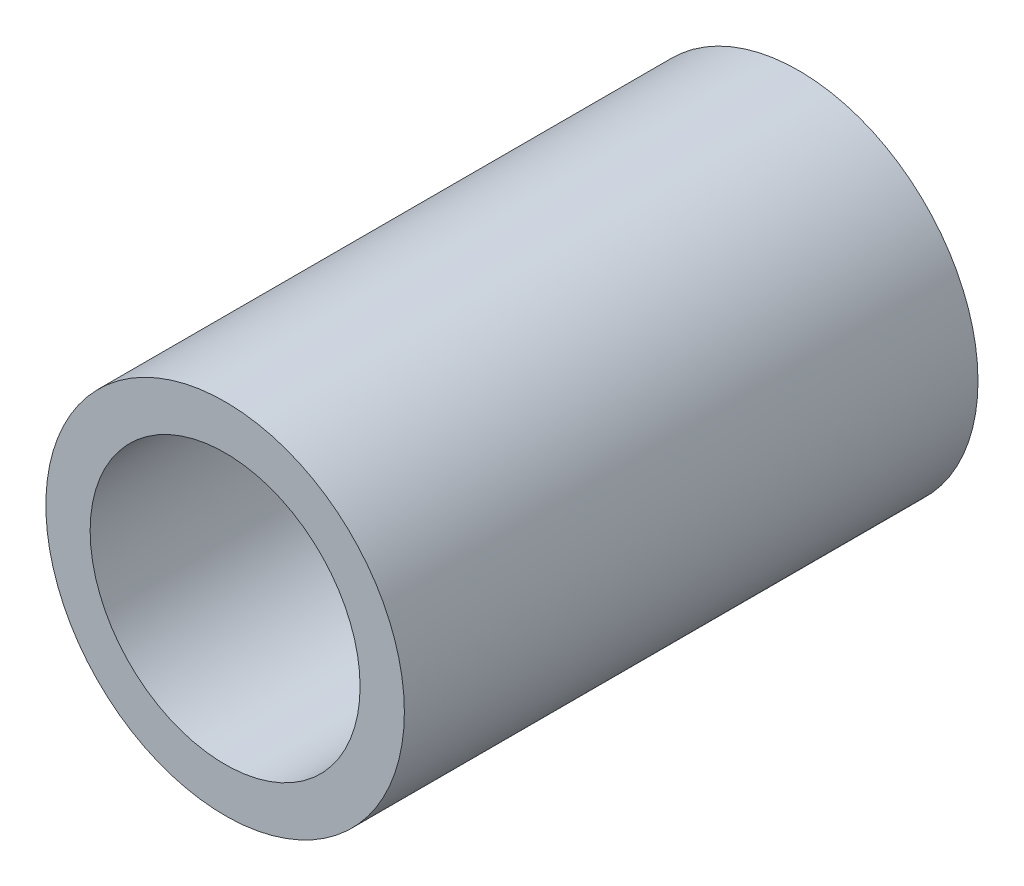
SolidWorks part; units mm, degrees
ref_plane "Plan de face" through (0, 0, 0) normal (0, 0, 1) x (1, 0, 0)
ref_plane "Plan de dessus" through (0, 0, 0) normal (0, 1, 0) x (1, 0, 0)
ref_plane "Plan de droite" through (0, 0, 0) normal (1, 0, 0) x (0, 0, -1)
sketch "Esquisse1" plane through (0, 0, 0) normal (0, 0, 1) x (1, 0, 0)
  line L0 (0, 0) -> (-619.8563, 51.5961) construction
  line L1 (0, 0) -> (-389.1874, 545.3743) construction
  line L2 (0, 0) -> (457.0972, 51.5961) construction
  line L3 (0, 0) -> (163.2386, 525.185) construction
  line L4 (132.0822, 424.9462) -> (457.0972, 51.5961) construction
  line L5 (-489.2424, 277.5909) -> (-355.5411, 635.4242) construction
  line L6 (-379.7372, 570.6665) -> (-22.8665, 389.9919) construction
  line L7 (-22.8665, 389.9919) -> (129.7077, 417.3067) construction
  dimension "D1" = 622
  dimension "D2" = 670
  dimension "D3" = 545
  dimension "D4" = 460
  dimension "D5" = 445
  dimension "D6" = 495
  dimension "D7" = 535
  dimension "D8" = 27
  dimension "D9" = 8
  dimension "D10" = 155
  dimension "D11" = 400
  dimension "D12" = 56
sketch "Esquisse2" plane through (0, 0, 0) normal (0, 0, 1) x (1, 0, 0)
  circle A0 centre (0, 0) radius 21.25
  circle A1 centre (0, 0) radius 16
  dimension "D1" = 42.5
  dimension "D2" = 32
extrude "Extrusion1" add sketch "Esquisse2" along normal mid plane 68
